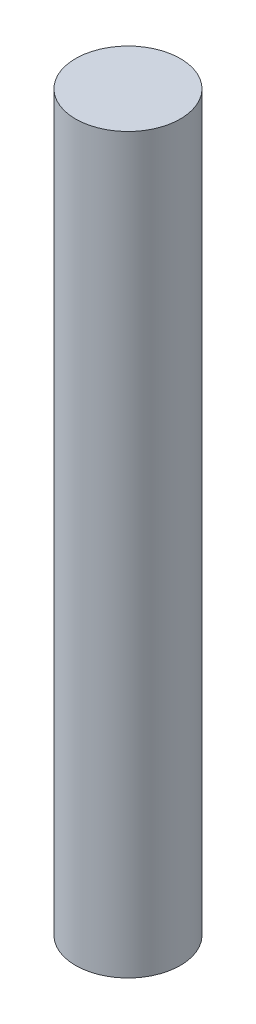
SolidWorks part; units mm, degrees
ref_plane "Front Plane" through (0, 0, 0) normal (0, 0, 1) x (1, 0, 0)
ref_plane "Top Plane" through (0, 0, 0) normal (0, 1, 0) x (1, 0, 0)
ref_plane "Right Plane" through (0, 0, 0) normal (1, 0, 0) x (0, 0, -1)
sketch "Sketch1" plane through (0, 0, 0) normal (0, 1, 0) x (1, 0, 0)
  circle A0 centre (0, 0) radius 0.635
  dimension "D1" = 1.27
extrude "Boss-Extrude1" add sketch "Sketch1" along normal mid plane 8.89
